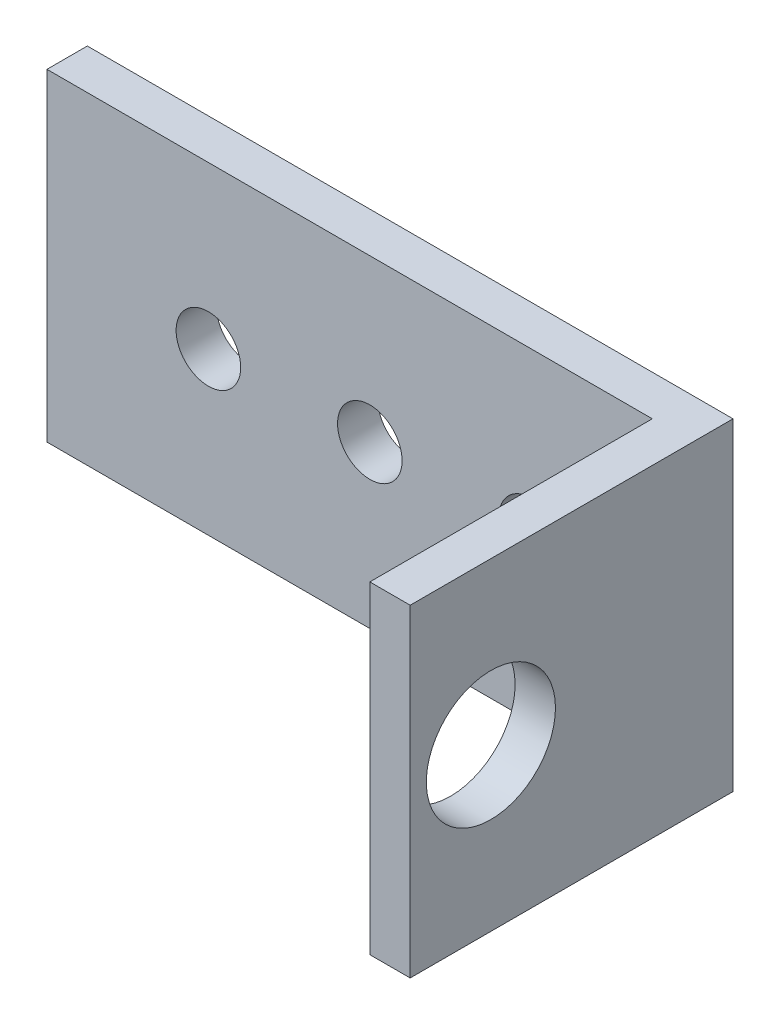
SolidWorks part; units mm, degrees
material "6061-T6 (SS)"
ref_plane "Front Plane" through (0, 0, 0) normal (0, 0, 1) x (1, 0, 0)
ref_plane "Top Plane" through (0, 0, 0) normal (0, 1, 0) x (1, 0, 0)
ref_plane "Right Plane" through (0, 0, 0) normal (1, 0, 0) x (0, 0, -1)
sketch "Sketch1" plane through (0, 0, 0) normal (0, 1, 0) x (1, 0, 0)
  line L1 (-25.4, -12.7) -> (25.4, -12.7)
  line L2 (-25.4, -12.7) -> (-25.4, 12.7)
  line L3 (-25.4, 12.7) -> (25.4, 12.7)
  line L4 (25.4, -12.7) -> (25.4, 12.7)
  line L5 (-25.4, -12.7) -> (25.4, 12.7) construction
  line L6 (-25.4, 12.7) -> (25.4, -12.7) construction
  line L7 (-25.4, -12.7) -> (22.225, -12.7)
  line L8 (-25.4, -12.7) -> (-25.4, 9.525)
  line L9 (-25.4, 9.525) -> (22.225, 9.525)
  line L10 (22.225, -12.7) -> (22.225, 9.525)
  point P0 (0, 0)
  dimension "D1" = 50.8
  dimension "D2" = 25.4
  dimension "D3" = 47.625
  dimension "D4" = 22.225
extrude "Boss-Extrude1" add sketch "Sketch1" along normal blind 25.4 contours L10 L1 L4 L3 L2 L9
sketch "Sketch2" plane through (25.4, 0, 0) normal (1, 0, 0) x (0, 0, -1)
  line L0 (12.7, 25.4) -> (12.7, 0) construction
  line L2 (-12.7, 0) -> (12.7, 0) construction
  circle A0 centre (-6.35, 12.7) radius 5.08
  dimension "D1" = 10.16
  dimension "D3" = 19.05
  dimension "D2" = 12.7
extrude "Cut-Extrude1" cut sketch "Sketch2" against normal up to surface (3.175 mm away) up to face at (22.225, 12.7, 1.5875)
sketch "Sketch3" plane through (0, 0, -9.525) normal (0, 0, 1) x (1, 0, 0)
  line L0 (-25.4, 25.4) -> (-25.4, 0) construction
  line L1 (-25.4, 0) -> (22.225, 0) construction
  circle A0 centre (-12.7, 12.7) radius 2.54
  circle A1 centre (0, 12.7) radius 2.54
  circle A2 centre (12.7, 12.7) radius 2.54
  dimension "D1" = 5.08
  dimension "D2" = 12.7
  dimension "D3" = 12.7
  dimension "D4" = 12.7
  dimension "D5" = 12.7
extrude "Cut-Extrude2" cut sketch "Sketch3" against normal up to surface (3.175 mm away) up to face at (0, 12.7, -12.7)
